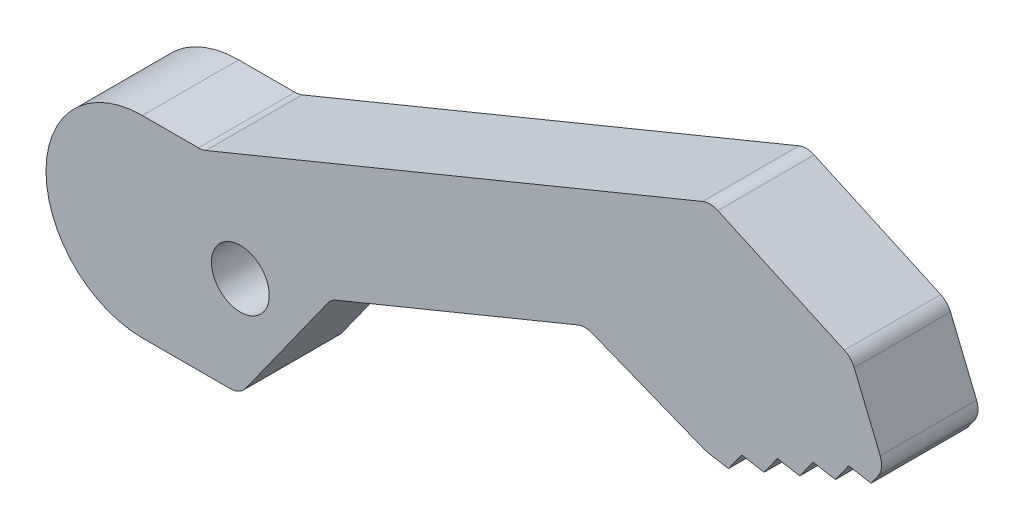
SolidWorks part; units mm, degrees
material "ABS"
ref_plane "Front Plane" through (0, 0, 0) normal (0, 0, 1) x (1, 0, 0)
ref_plane "Top Plane" through (0, 0, 0) normal (0, 1, 0) x (1, 0, 0)
ref_plane "Right Plane" through (0, 0, 0) normal (1, 0, 0) x (0, 0, -1)
sketch "Sketch1" plane through (0, 0, 0) normal (0, 0, 1) x (1, 0, 0)
  line L0 (0, 0) -> (22, 0) construction
  line L1 (0, 5) -> (22, 5)
  line L2 (0, -5) -> (22, -5)
  line L3 (20.05, 5) -> (23.9914, -4.5863) construction
  line L4 (20.05, 5) -> (51.4959, 17.929) construction
  line L5 (23.9914, -4.5863) -> (55.4373, 8.3426) construction
  line L6 (51.4959, 17.929) -> (55.4373, 8.3426) construction
  line L7 (20.05, 5) -> (46.409, 15.8375)
  line L8 (46.409, 15.8375) -> (53.7261, 12.5046)
  line L9 (53.7261, 12.5046) -> (55.4373, 8.3426)
  line L10 (46.1885, 4.54) -> (39.9002, 7.0361)
  line L11 (39.9002, 7.0361) -> (26.7299, 1.6211)
  line L12 (46.1885, 4.54) -> (55.4373, 8.3426) construction
  line L13 (46.1885, 4.54) -> (47.3529, 4.3376)
  line L14 (47.3529, 4.3376) -> (48.0382, 5.3005)
  line L15 (47.3529, 4.3376) -> (54.752, 7.3797) construction
  line L16 (48.0382, 5.3005) -> (49.2027, 5.0981)
  line L17 (49.2027, 5.0981) -> (49.888, 6.0611)
  line L18 (49.888, 6.0611) -> (51.0524, 5.8587)
  line L19 (51.0524, 5.8587) -> (51.7378, 6.8216)
  line L20 (51.7378, 6.8216) -> (52.9022, 6.6192)
  line L21 (52.9022, 6.6192) -> (53.5875, 7.5821)
  line L22 (53.5875, 7.5821) -> (54.752, 7.3797)
  line L23 (54.752, 7.3797) -> (55.4373, 8.3426)
  line L24 (26.7299, 1.6211) -> (22, -5)
  arc A0 (0, 5) -> (0, -5) centre (0, 0) ccw
  arc A1 (22, -5) -> (22, 5) centre (22, 0) ccw
  circle A2 centre (0, 0) radius 1.5
  circle A3 centre (22.0207, 0.2068) radius 1.5
  point P3 (11, 0)
  dimension "D11" = 3
  dimension "D1" = 10
  dimension "D2" = 22
  dimension "D3" = 157.65
  dimension "D4" = 1.95
  dimension "D5" = 34
  dimension "D6" = 5.5
  dimension "D7" = 4.5
  dimension "D8" = 10
  dimension "D9" = 136
  dimension "D10" = 14.24
  dimension "D12" = 2
  dimension "D13" = 0.63
  dimension "D14" = 8
extrude "Boss-Extrude3" add sketch "Sketch1" along normal blind 5 contours A1 L1 A0 L2 A3 A2 | A1 L11 L10 L13 L14 L16 L17 L18 L19 L20 L21 L22 L23 L9 L8 L7 L1
fillet "Fillet1" radius 1 8 edges at (46.1885, 4.54, 2.5) (39.9002, 7.0361, 2.5) (53.7261, 12.5046, 2.5) (55.4373, 8.3426, 2.5) (46.409, 15.8375, 2.5) (20.05, 5, 2.5) (26.7299, 1.6211, 2.5) (22, -5, 2.5)
sketch "Sketch4" plane through (0, 0, 0) normal (0, 0, -1) x (-1, 0, 0)
  line L0 (0, 5) -> (-19.8524, 5) construction
  line L1 (0, -5) -> (-21.4854, -5) construction
  line L2 (-16.9363, -5) -> (9.1673, -5)
  line L3 (9.1673, -5) -> (9.1673, 5)
  line L4 (9.1673, 5) -> (-16.9363, 5)
  arc A0 (-16.9363, 5) -> (-16.9363, -5) centre (-16.9363, 0) cw
extrude "Cut-Extrude2" cut sketch "Sketch4" against normal blind 5 contours L3 L4 A0 L2
